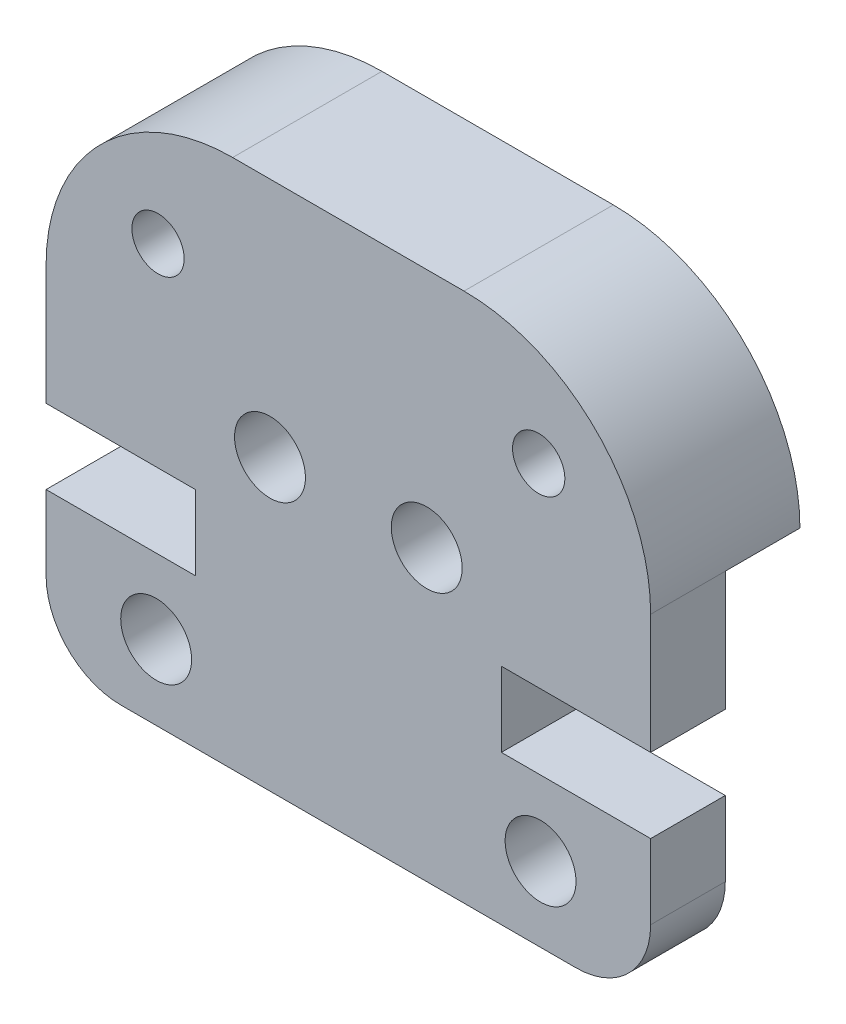
SolidWorks part; units mm, degrees
ref_plane "Front Plane" through (0, 0, 0) normal (0, 0, 1) x (1, 0, 0)
ref_plane "Top Plane" through (0, 0, 0) normal (0, 1, 0) x (1, 0, 0)
ref_plane "Right Plane" through (0, 0, 0) normal (1, 0, 0) x (0, 0, -1)
sketch "Sketch1" plane through (0, 0, 0) normal (0, 0, 1) x (1, 0, 0)
  line L0 (8.1, 14.205) -> (8.1, 0) construction
  line L1 (12.2, 4) -> (16.2, 4)
  line L2 (12.2, 6) -> (12.2, 4)
  line L3 (16.2, 6) -> (12.2, 6)
  line L4 (16.2, 2) -> (16.2, 4)
  line L5 (16.2, 9.205) -> (16.2, 6)
  line L14 (0, 9.205) -> (0, 6)
  line L15 (5, 14.205) -> (11.2, 14.205)
  line L16 (2, 0) -> (14.2, 0)
  line L18 (0, 2) -> (0, 4)
  line L19 (0, 6) -> (4, 6)
  line L21 (4, 6) -> (4, 4)
  line L22 (4, 4) -> (0, 4)
  circle A0 centre (13.25, 2) radius 0.95
  arc A1 (16.2, 2) -> (14.2, 0) centre (14.2, 2) cw
  circle A2 centre (13.2, 11.205) radius 0.7
  arc A3 (11.2, 14.205) -> (16.2, 9.205) centre (11.2, 9.205) cw
  circle A4 centre (10.2, 7.75) radius 0.95
  circle A11 centre (6, 7.75) radius 0.95
  arc A13 (5, 14.205) -> (0, 9.205) centre (5, 9.205) ccw
  circle A15 centre (3, 11.205) radius 0.7
  arc A17 (0, 2) -> (2, 0) centre (2, 2) ccw
  circle A19 centre (2.95, 2) radius 0.95
  dimension "D1" = 1.4
  dimension "D2" = 1.9
  dimension "D3" = 5
  dimension "D4" = 2
  dimension "D5" = 3
  dimension "D6" = 6
  dimension "D7" = 8.1
  dimension "D8" = 7.75
  dimension "D9" = 3
  dimension "D10" = 14.205
extrude "Boss-Extrude1" add sketch "Sketch1" along normal blind 4
sketch "Sketch2" plane through (0, 0, 0) normal (0, 0, -1) x (-1, 0, 0)
  line L0 (0, 0) -> (0, 9.205)
  line L1 (0, 9.205) -> (-16.2, 9.205)
  line L2 (-16.2, 9.205) -> (-16.2, 0)
  line L3 (-16.2, 0) -> (0, 0)
extrude "Cut-Extrude1" cut sketch "Sketch2" against normal blind 2
equation "\"D7@Sketch1\"= \"fingerWidth@parametersSketch@prostheticParameters.SLDPRT\" / 2 'DIP width"
equation "\"D10@Sketch1\"= \"HL@parametersSketch@prostheticParameters.SLDPRT\" * 0.093 - 3 'DIP length - Sil. Sht DIP"
equation "\"D1@Sketch1\"= 1 + \"tol1@parametersSketch@prostheticParameters.SLDPRT\""
equation "\"D2@Sketch1\"= 1.5 + \"tol1@parametersSketch@prostheticParameters.SLDPRT\""
